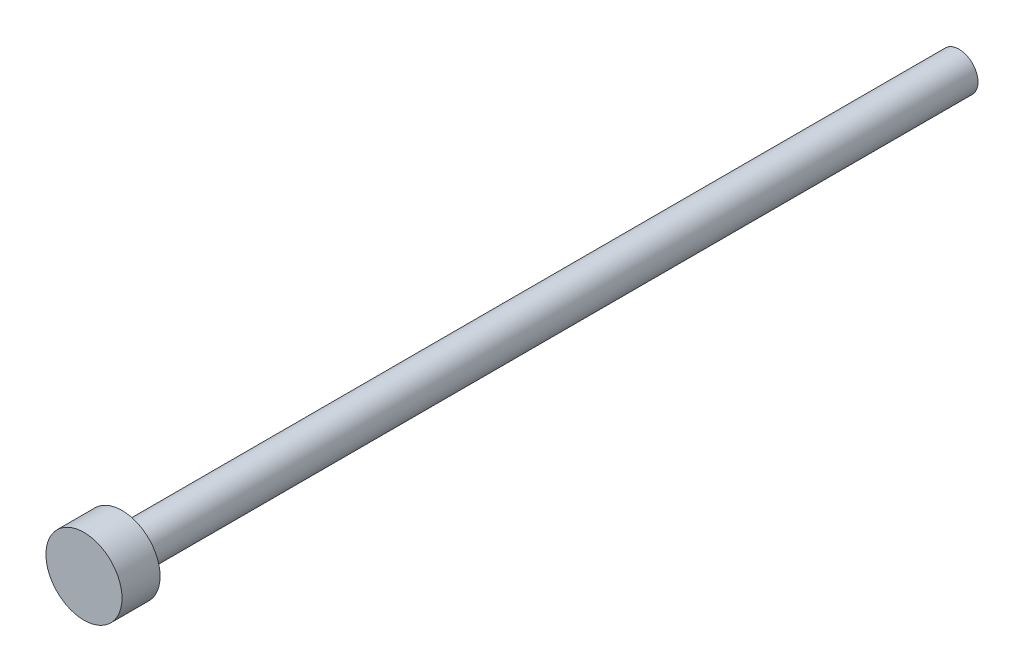
SolidWorks part; units mm, degrees
ref_plane "Front Plane" through (0, 0, 0) normal (0, 0, 1) x (1, 0, 0)
ref_plane "Top Plane" through (0, 0, 0) normal (0, 1, 0) x (1, 0, 0)
ref_plane "Right Plane" through (0, 0, 0) normal (1, 0, 0) x (0, 0, -1)
sketch "Sketch2" plane through (0, 0, 0) normal (0, 0, 1) x (1, 0, 0)
  circle A0 centre (0, 0) radius 0.5
extrude "Boss-Extrude2" add sketch "Sketch2" along normal blind 22
sketch "Sketch3" plane through (0, 0, 22) normal (0, 0, 1) x (1, 0, 0)
  circle A0 centre (0, 0) radius 1
extrude "Boss-Extrude3" add sketch "Sketch3" along normal blind 1
